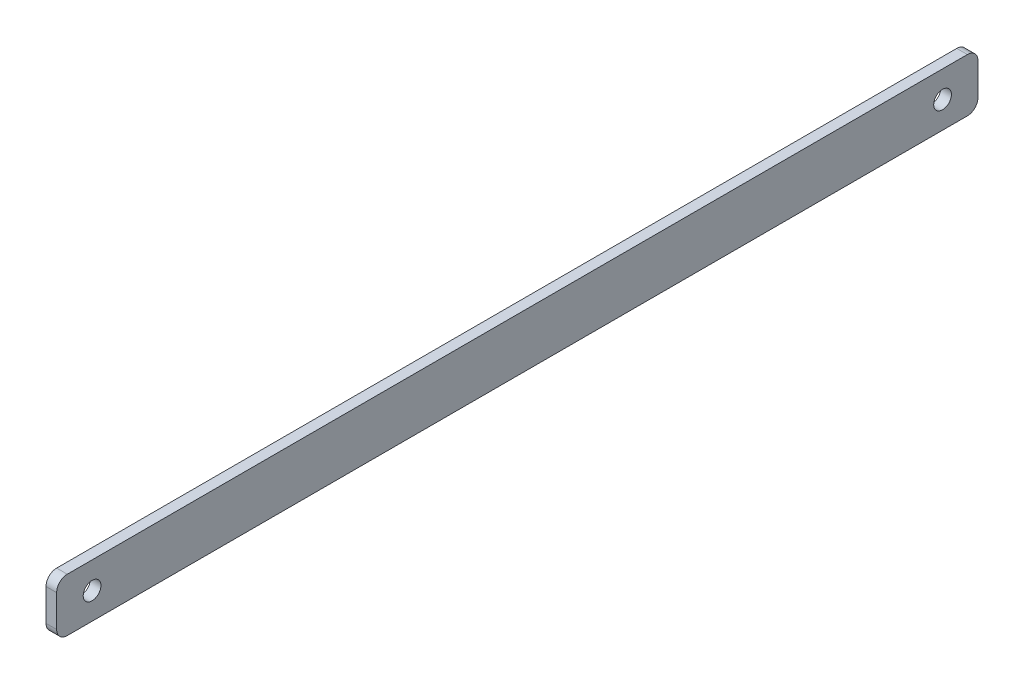
SolidWorks part; units mm, degrees
ref_plane "Спереди" through (0, 0, 0) normal (0, 0, 1) x (1, 0, 0)
ref_plane "Сверху" through (0, 0, 0) normal (0, 1, 0) x (1, 0, 0)
ref_plane "Справа" through (0, 0, 0) normal (1, 0, 0) x (0, 0, -1)
sketch "Эскиз1" plane through (0, 0, 0) normal (1, 0, 0) x (0, 0, -1)
  line L0 (0, 26.4372) -> (0, -27.3449) construction
  line L1 (-127, 7.5) -> (127, 7.5)
  line L2 (-130, 4.5) -> (-130, -4.5)
  line L3 (-127, -7.5) -> (127, -7.5)
  line L4 (130, 4.5) -> (130, -4.5)
  line L5 (-130, 7.5) -> (130, -7.5) construction
  line L6 (-130, -7.5) -> (130, 7.5) construction
  circle A0 centre (-120, 0) radius 2.5
  circle A1 centre (120, 0) radius 2.5
  arc A2 (-130, -4.5) -> (-127, -7.5) centre (-127, -4.5) ccw
  arc A3 (127, 7.5) -> (130, 4.5) centre (127, 4.5) cw
  arc A4 (127, -7.5) -> (130, -4.5) centre (127, -4.5) ccw
  arc A5 (-127, 7.5) -> (-130, 4.5) centre (-127, 4.5) ccw
  point P0 (0, 0)
  point P24 (0, 0)
  dimension "D1" = 3
extrude "Бобышка-Вытянуть1" add sketch "Эскиз1" along normal blind 3
